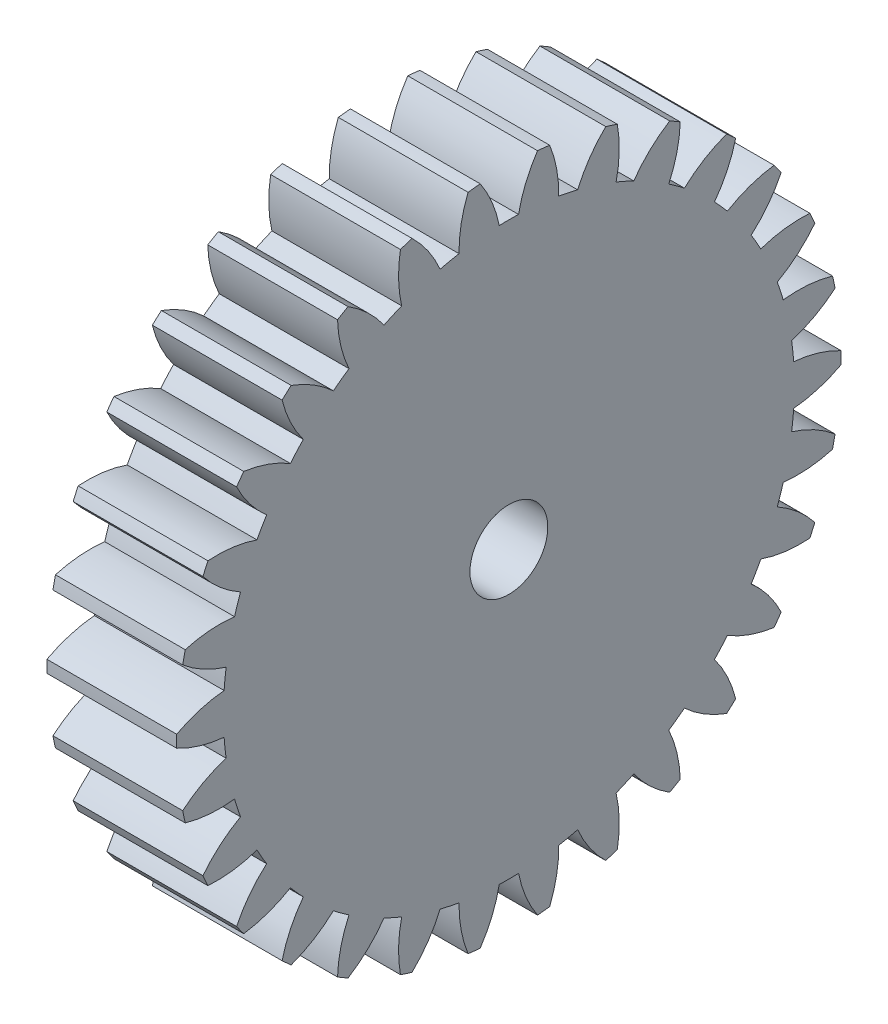
SolidWorks part; units mm, degrees
ref_plane "Plane1" through (0, 0, 0) normal (0, 0, 1) x (1, 0, 0)
ref_plane "Plane2" through (0, 0, 0) normal (0, 1, 0) x (1, 0, 0)
ref_plane "Plane3" through (0, 0, 0) normal (1, 0, 0) x (0, 0, -1)
other "Configuration Table"
sketch "HoldingSke" plane through (0, 0, 0) normal (0, 1, 0) x (1, 0, 0)
  line L0 (0, 0) -> (1.0825, -0.625)
  line L1 (-15, 0) -> (100, 0) construction
  line L2 (0, 0) -> (-2.1039, 2.3779)
  line L3 (0, 0) -> (-11.863, 4.5341)
  line L4 (0, 0) -> (7.479, 4.318)
  line L5 (0, 0) -> (-46.8476, -17.4728)
  line L6 (0, 0) -> (-4.1448, -2.7965)
  line L7 (-2.1039, 2.3779) -> (8.6586, 51.2059)
  line L8 (-76.2, 54.61) -> (-75.7, 54.61)
  line L9 (-71.009, 38.7566) -> (-53.1078, 45.2721)
  line L10 (-76.2, 71.12) -> (104.1128, 71.12)
  line L11 (0, 0) -> (-5, 0)
  line L12 (-76.2, 101.6) -> (-76.17, 101.6)
  line L13 (24.9733, 27.94) -> (52.9518, 28.4284)
  line L14 (24.9733, 27.94) -> (24.9743, 27.94)
  line L15 (24.9733, 27.94) -> (100.4006, 29.5858)
  line L16 (-63.627, -0.8) -> (-12.827, -0.8)
  circle A0 centre (0, 0) radius 1.5
  circle A1 centre (0, 0) radius 10.999
  circle A2 centre (0, 0) radius 37.5
  circle A3 centre (0, 0) radius 1.5
  dimension "MHD" = 21.998
  dimension "Hub_dia" = 75
  dimension "Bore" = 3
  dimension "MBD" = 3
  dimension "Num_teeth" = 30
  dimension "Pitch" = 1.25
  dimension "Overall_len" = 50
  dimension "Show_teeth" = 30
  dimension "Thickness" = 5
  dimension "OAL" = 50.0001
  dimension "T_dim" = 0.5
  dimension "Ap" = 20
  dimension "H" = 19.05
  dimension "Pitch_radius" = 180.3128
  dimension "Width" = 5
  dimension "Backlash" = 0.03
  dimension "Addendum_fac" = 1
  dimension "Dedendum_fac" = 1.25
  dimension "Clearance_fac" = 0.25
  dimension "Dedendum_add" = 0.001
  dimension "Module" = 0.8
sketch "BasProSke" plane through (0, 0, 0) normal (0, 1, 0) x (1, 0, 0)
  line L0 (-10, 0) -> (60, 0) construction
  line L1 (0, 0) -> (0, 12.8)
  line L2 (0, 0) -> (5, 0)
  line L3 (5, 0) -> (5, 12.8)
  line L4 (5, 12.8) -> (0, 12.8)
  dimension "Thickness" = 5
  dimension "Diameter" = 25.6
revolve "Base-Revolve" add sketch "BasProSke" angle 360 about L0
sketch "TooCutSke" plane through (0, 0, 0) normal (1, 0, 0) x (0, 0, -1)
  line L1 (0, 0) -> (0, 107) construction
  line L2 (0, 0) -> (-0.6805, 11.9807) construction
  line L3 (0, 0) -> (-2.5058, 23.8411) construction
  line L4 (-0.6805, 11.9807) -> (-1.2529, 11.9205) construction
  arc A0 (0.3724, 10.9927) -> (-0.3724, 10.9927) centre (0, 0) ccw
  arc A1 (1.1205, 12.7764) -> (-1.1205, 12.7764) centre (0, 0) ccw
  circle A2 centre (0, 0) radius 12 construction
  circle A3 centre (0, 0) radius 11.2763 construction
  arc A4 (-0.3724, 10.9927) -> (-1.1205, 12.7764) centre (-5.0822, 10.0661) ccw
  arc A5 (1.1205, 12.7764) -> (0.3724, 10.9927) centre (5.0822, 10.0661) ccw
  dimension "Root_dia" = 21.998
  dimension "Overcut_dia" = 25.6508
  dimension "Pitch_dia" = 24
  dimension "Base_dia" = 22.5526
  dimension "Flank_rad" = 4.8
  dimension "Half_ang" = 6
  dimension "Half_CT" = 0.5755
extrude "ToothCut" cut sketch "TooCutSke" along normal through all
fillet "Breaks" [suppressed] radius 0.016
fillet "RootFillets" [suppressed] radius 0.201
pattern_circular "TeethCuts" count 30 every 12 about axis through (-10, 0, 0) along (1, 0, 0) of "ToothCut", "RootFillets", "Breaks"
sketch "HubNeaOneSke" plane through (0, 0, 0) normal (-1, 0, 0) x (0, 0, 1)
  circle A0 centre (0, 0) radius 10.999
  dimension "Diameter" = 21.998
extrude "HubNearOne" [suppressed] add sketch "HubNeaOneSke" along normal blind 45.0001
sketch "HubNeaBotSke" plane through (0, 0, 0) normal (-1, 0, 0) x (0, 0, 1)
  circle A0 centre (0, 0) radius 10.999
  dimension "Diameter" = 21.998
extrude "HubNearBoth" [suppressed] add sketch "HubNeaBotSke" along normal blind 22.5
ref_plane "FarPln" through (5, 0, 0) normal (1, 0, 0) x (0, 0, -1)
sketch "HubFarSke" plane through (5, 0, 0) normal (1, 0, 0) x (0, 0, -1)
  circle A0 centre (0, 0) radius 10.999
  dimension "Diameter" = 21.998
extrude "HubFar" [suppressed] add sketch "HubFarSke" along normal blind 22.5
sketch "BorSke" plane through (0, 0, 0) normal (1, 0, 0) x (0, 0, -1)
  circle A0 centre (0, 0) radius 1.5
  dimension "Diameter" = 3
extrude "Bore" cut sketch "BorSke" along normal mid plane 100.0001
sketch "KeySke" plane through (0, 0, 0) normal (1, 0, 0) x (0, 0, -1)
  line L0 (-0.6, 0) -> (-0.6, 2)
  line L1 (-0.6, 2) -> (0.6, 2)
  line L2 (0.6, 2) -> (0.6, 0)
  line L3 (0, 0) -> (0, 34) construction
  line L4 (-0.6, 0) -> (0.6, 0)
  dimension "Offset" = 2
  dimension "Width" = 1.2
extrude "Keyway" [suppressed] cut sketch "KeySke" along normal mid plane 100.0001
pattern_circular "Keyway2" [suppressed] count 2 every 90 about axis through (-10, 0, 0) along (1, 0, 0)
sketch "草图1" plane through (5, 0, 0) normal (1, 0, 0) x (0, 0, -1)
  circle A0 centre (0, 0) radius 12 construction
  dimension "D1" = 24
equation "' \"Module@HoldingSke\" = 6.35"
equation "' \"Num_teeth@HoldingSke\" = 12"
equation "' \"Ap@HoldingSke\" =  20"
equation "' \"Ap@HoldingSke\" = 20"
equation "' \"Width@HoldingSke\" = 0.5 * 25.4"
equation "' \"Hub_dia@HoldingSke\"= 1 * 25.4"
equation "' \"Hub_dia@HoldingSke\" = 1 * 25.4"
equation "' \"Overall_len@HoldingSke\" = 1.0 * 25.4"
equation "' \"Bore@HoldingSke\" = 0.75 * 25.4"
equation "' \"T_dim@HoldingSke\" = 0.1 * 25.4"
equation "' \"Width@KeySke\" = 0.25 * 25.4"
equation "' \"Show_teeth@HoldingSke\" = 13"
equation "' \"Backlash@HoldingSke\" = 0.009 * 25.4"
equation "' \"Addendum_fac@HoldingSke\" = 1.0"
equation "' \"Dedendum_fac@HoldingSke\" = 1.25"
equation "' \"Dedendum_add@HoldingSke\" = 0.00005 * 25.4"
equation "' \"Clearance_fac@HoldingSke\" = 0.25"
equation "\"Pitch@HoldingSke\" = 1 / \"Module@HoldingSke\""
equation "\"Overcut_dia@TooCutSke\" = (\"Num_teeth@HoldingSke\" + 2 * \"Addendum_fac@HoldingSke\") / \"Pitch@HoldingSke\" + 0.002 * 25.4"
equation "\"Pitch_dia@TooCutSke\" = \"Num_teeth@HoldingSke\" / \"Pitch@HoldingSke\""
equation "\"Base_dia@TooCutSke\" = \"Num_teeth@HoldingSke\" / \"Pitch@HoldingSke\" * cos((\"Ap@HoldingSke\"  * 3.14159265 / 180))"
equation "\"Root_dia@TooCutSke\" = (\"Num_teeth@HoldingSke\" + 2) / \"Pitch@HoldingSke\" - 2 * (\"Addendum_fac@HoldingSke\" + \"Dedendum_fac@HoldingSke\") / \"Pitch@HoldingSke\" - \"Dedendum_add@HoldingSke\" * 2"
equation "\"Half_ang@TooCutSke\" = 180 / \"Num_teeth@HoldingSke\""
equation "\"Half_CT@TooCutSke\" = \"Num_teeth@HoldingSke\" / \"Pitch@HoldingSke\" * sin((3.14159265 / 2 / \"Num_teeth@HoldingSke\")) / 2 - 7 * \"Backlash@HoldingSke\" / 4"
equation "\"Flank_rad@TooCutSke\" = \"Num_teeth@HoldingSke\" / \"Pitch@HoldingSke\" / 5"
equation "\"Radius@RootFillets\" = \"Clearance_fac@HoldingSke\" / \"Pitch@HoldingSke\" + \"Dedendum_add@HoldingSke\""
equation "\"Break_rad@Breaks\" = 0.02 / \"Pitch@HoldingSke\""
equation "\"Thickness@HoldingSke\" = \"Width@HoldingSke\""
equation "\"OAL@HoldingSke\" = \"Thickness@HoldingSke\""
equation "\"MHD@HoldingSke\" = (\"Num_teeth@HoldingSke\" + 2) / \"Pitch@HoldingSke\" - 2 * (\"Addendum_fac@HoldingSke\" + \"Dedendum_fac@HoldingSke\")  / \"Pitch@HoldingSke\" - \"Dedendum_add@HoldingSke\" * 2"
equation "\"MBD@HoldingSke\" = (\"Num_teeth@HoldingSke\" + 2) / \"Pitch@HoldingSke\" - 2 * (\"Addendum_fac@HoldingSke\" + \"Dedendum_fac@HoldingSke\")  / \"Pitch@HoldingSke\" - \"Dedendum_add@HoldingSke\" * 2 - 0.002 * 25.4"
equation "\"MHD@HoldingSke\" = ((sgn( \"MHD@HoldingSke\" - \"Hub_dia@HoldingSke\" )-1)*( \"MHD@HoldingSke\" - \"Hub_dia@HoldingSke\" ))/-2+ \"Hub_dia@HoldingSke\""
equation "\"MBD@HoldingSke\" = ((sgn( \"MBD@HoldingSke\" - \"Bore@HoldingSke\" )-1)*( \"MBD@HoldingSke\" - \"Bore@HoldingSke\" ))/-2+ \"Bore@HoldingSke\""
equation "\"OAL@HoldingSke\" = ((sgn( \"OAL@HoldingSke\" - \"Overall_len@HoldingSke\" )+1)*( \"OAL@HoldingSke\" - \"Overall_len@HoldingSke\" ))/2 + \"Overall_len@HoldingSke\" + 0.000002 * 25.4"
equation "\"Num_teeth@TeethCuts\" = int( \"Show_teeth@HoldingSke\" ) + 1"
equation "\"Num_teeth@TeethCuts\" = ((sgn( \"Num_teeth@TeethCuts\" - \"Num_teeth@HoldingSke\" )-1)*( \"Num_teeth@TeethCuts\" - \"Num_teeth@HoldingSke\" ))/-2+ \"Num_teeth@HoldingSke\""
equation "\"Num_teeth@TeethCuts\" = ((sgn( \"Num_teeth@TeethCuts\" - 2.0)+1)*( \"Num_teeth@TeethCuts\" - 2.0))/2 +2.0"
equation "\"Angle@TeethCuts\" = 360.0 / \"Num_teeth@HoldingSke\""
equation "\"Diameter@BasProSke\" = (\"Num_teeth@HoldingSke\" + 2 * \"Addendum_fac@HoldingSke\") / \"Pitch@HoldingSke\""
equation "\"Thickness@BasProSke\"  = \"Thickness@HoldingSke\""
equation "' \"Fillet_rad@BasProSke\" =  \"Thickness@HoldingSke\" * 0.05"
equation "' \"Fillet_rad@BasProSke\" = \"Thickness@HoldingSke\" * 0.05"
equation "\"MHD@HoldingSke\" = ((sgn( \"MHD@HoldingSke\" - \"Root_dia@TooCutSke\" )-1)*( \"MHD@HoldingSke\" - \"Root_dia@TooCutSke\" ))/-2+ \"Root_dia@TooCutSke\""
equation "\"Diameter@HubNeaOneSke\" = \"MHD@HoldingSke\""
equation "\"Length@HubNearOne\" = \"OAL@HoldingSke\" - \"Thickness@BasProSke\""
equation "\"Diameter@HubNeaBotSke\" = \"MHD@HoldingSke\""
equation "\"Length@HubNearBoth\" = ( \"OAL@HoldingSke\" - \"Thickness@BasProSke\" ) / 2.0"
equation "\"Thickness@FarPln\" = \"Thickness@BasProSke\""
equation "\"Diameter@HubFarSke\" = \"MHD@HoldingSke\""
equation "\"Length@HubFar\" = ( \"OAL@HoldingSke\" - \"Thickness@BasProSke\" ) / 2.0"
equation "\"Diameter@BorSke\" = \"MBD@HoldingSke\""
equation "\"D1@Bore\" = \"OAL@HoldingSke\" * 2.0"
equation "\"D1@Keyway\" = \"OAL@HoldingSke\" * 2.0"
equation "\"Offset@KeySke\" = \"T_dim@HoldingSke\" + \"MBD@HoldingSke\" / 2.0"
